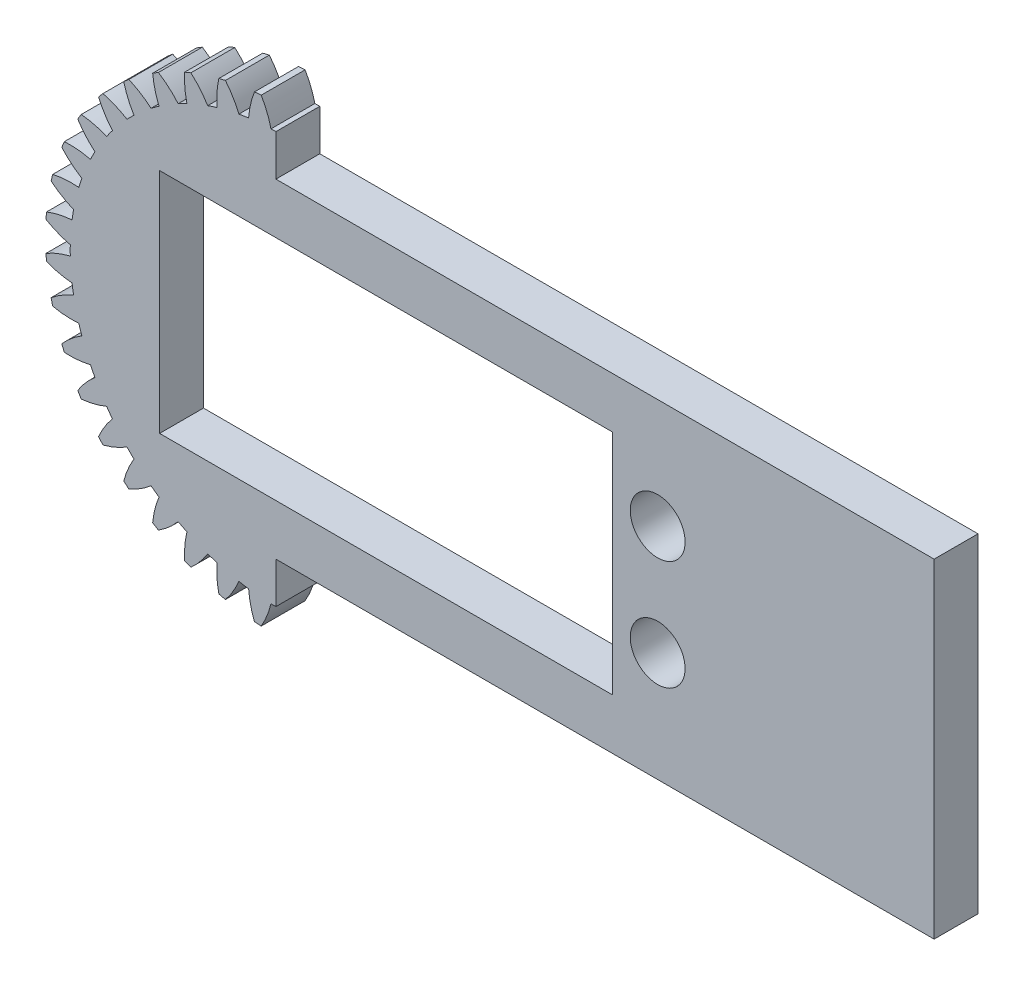
SolidWorks part; units mm, degrees
ref_plane "Front Plane" through (0, 0, 0) normal (0, 0, 1) x (1, 0, 0)
ref_plane "Top Plane" through (0, 0, 0) normal (0, 1, 0) x (1, 0, 0)
ref_plane "Right Plane" through (0, 0, 0) normal (1, 0, 0) x (0, 0, -1)
sketch "Model" plane through (0, 0, 0) normal (0, 0, 1) x (1, 0, 0)
  arc A0 (99.0731, 84.9083) -> (99.0247, 84.2939) centre (119.9819, 82.9536) ccw
  arc A1 (101.3989, 85.4426) -> (99.0731, 84.9083) centre (102.0071, 77.4658) ccw
  arc A2 (101.5392, 86.3289) -> (101.3989, 85.4426) centre (119.9819, 82.9536) ccw
  arc A3 (99.4924, 87.5558) -> (101.5392, 86.3289) centre (104.5827, 93.7274) ccw
  arc A4 (99.6363, 88.1551) -> (99.4924, 87.5558) centre (119.9819, 82.9536) ccw
  arc A5 (102.017, 88.319) -> (99.6363, 88.1551) centre (101.37, 80.3452) ccw
  arc A6 (102.2943, 89.1725) -> (102.017, 88.319) centre (119.9819, 82.9536) ccw
  arc A7 (100.4646, 90.7044) -> (102.2943, 89.1725) centre (106.4577, 96.0037) ccw
  arc A8 (100.7005, 91.2739) -> (100.4646, 90.7044) centre (119.9819, 82.9536) ccw
  arc A9 (103.0775, 91.0633) -> (100.7005, 91.2739) centre (101.1911, 83.2889) ccw
  arc A10 (103.4849, 91.8628) -> (103.0775, 91.0633) centre (119.9819, 82.9536) ccw
  arc A11 (101.9174, 93.6622) -> (103.4849, 91.8628) centre (108.6657, 97.9587) ccw
  arc A12 (102.2394, 94.1877) -> (101.9174, 93.6622) centre (119.9819, 82.9536) ccw
  arc A13 (104.5543, 93.6079) -> (102.2394, 94.1877) centre (101.4748, 86.2243) ccw
  arc A14 (105.0817, 94.3339) -> (104.5543, 93.6079) centre (119.9819, 82.9536) ccw
  arc A15 (103.815, 96.3562) -> (105.0817, 94.3339) centre (111.1523, 99.5442) ccw
  arc A16 (104.2153, 96.8249) -> (103.815, 96.3562) centre (119.9819, 82.9536) ccw
  arc A17 (106.4109, 95.8901) -> (104.2153, 96.8249) centre (102.2143, 89.0792) ccw
  arc A18 (107.0454, 96.5247) -> (106.4109, 95.8901) centre (119.9819, 82.9536) ccw
  arc A19 (106.1106, 98.7203) -> (107.0454, 96.5247) centre (113.8564, 100.7212) ccw
  arc A20 (106.5793, 99.1206) -> (106.1106, 98.7203) centre (119.9819, 82.9536) ccw
  arc A21 (108.6017, 97.8538) -> (106.5793, 99.1206) centre (103.3913, 91.7832) ccw
  arc A22 (109.3277, 98.3813) -> (108.6017, 97.8538) centre (119.9819, 82.9536) ccw
  arc A23 (108.7479, 100.6961) -> (109.3277, 98.3813) centre (116.7112, 101.4607) ccw
  arc A24 (109.2734, 101.0182) -> (108.7479, 100.6961) centre (119.9819, 82.9536) ccw
  arc A25 (111.0727, 99.4506) -> (109.2734, 101.0182) centre (104.9769, 94.2699) ccw
  arc A26 (111.8723, 99.858) -> (111.0727, 99.4506) centre (119.9819, 82.9536) ccw
  arc A27 (111.6617, 102.2351) -> (111.8723, 99.858) centre (119.6467, 101.7445) ccw
  arc A28 (112.2311, 102.471) -> (111.6617, 102.2351) centre (119.9819, 82.9536) ccw
  arc A29 (113.7631, 100.6412) -> (112.2311, 102.471) centre (106.9318, 96.4779) ccw
  arc A30 (114.6165, 100.9185) -> (113.7631, 100.6412) centre (119.9819, 82.9536) ccw
  arc A31 (114.7804, 103.2993) -> (114.6165, 100.9185) centre (122.5903, 101.5656) ccw
  arc A32 (115.3798, 103.4432) -> (114.7804, 103.2993) centre (119.9819, 82.9536) ccw
  arc A33 (116.6066, 101.3963) -> (115.3798, 103.4432) centre (109.2082, 98.3528) ccw
  arc A34 (117.4929, 101.5367) -> (116.6066, 101.3963) centre (119.9819, 82.9536) ccw
  arc A35 (118.0272, 103.8625) -> (117.4929, 101.5367) centre (125.4698, 100.9284) ccw
  arc A36 (118.6417, 103.9108) -> (118.0272, 103.8625) centre (119.9819, 82.9536) ccw
  arc A37 (119.5332, 101.6973) -> (118.6417, 103.9108) centre (111.7498, 99.8486) ccw
  arc A38 (120.4306, 101.6973) -> (119.5332, 101.6973) centre (119.9819, 82.9536) ccw
  arc A39 (121.3221, 103.9108) -> (120.4306, 101.6973) centre (128.2141, 99.8486) ccw
  arc A40 (121.9366, 103.8625) -> (121.3221, 103.9108) centre (119.9819, 82.9536) ccw
  arc A41 (122.4709, 101.5367) -> (121.9366, 103.8625) centre (114.4941, 100.9284) ccw
  arc A42 (123.3572, 101.3963) -> (122.4709, 101.5367) centre (119.9819, 82.9536) ccw
  arc A43 (124.5841, 103.4432) -> (123.3572, 101.3963) centre (130.7557, 98.3528) ccw
  arc A44 (125.1834, 103.2993) -> (124.5841, 103.4432) centre (119.9819, 82.9536) ccw
  arc A45 (125.3473, 100.9185) -> (125.1834, 103.2993) centre (117.3735, 101.5656) ccw
  arc A46 (126.2007, 100.6412) -> (125.3473, 100.9185) centre (119.9819, 82.9536) ccw
  arc A47 (127.7327, 102.471) -> (126.2007, 100.6412) centre (133.032, 96.4779) ccw
  arc A48 (128.3021, 102.2351) -> (127.7327, 102.471) centre (119.9819, 82.9536) ccw
  arc A49 (128.0916, 99.858) -> (128.3021, 102.2351) centre (120.3172, 101.7445) ccw
  arc A50 (128.8911, 99.4506) -> (128.0916, 99.858) centre (119.9819, 82.9536) ccw
  arc A51 (130.6904, 101.0182) -> (128.8911, 99.4506) centre (134.987, 94.2699) ccw
  arc A52 (131.216, 100.6961) -> (130.6904, 101.0182) centre (119.9819, 82.9536) ccw
  arc A53 (130.6362, 98.3813) -> (131.216, 100.6961) centre (123.2526, 101.4607) ccw
  arc A54 (131.3621, 97.8538) -> (130.6362, 98.3813) centre (119.9819, 82.9536) ccw
  arc A55 (133.3845, 99.1206) -> (131.3621, 97.8538) centre (136.5725, 91.7832) ccw
  arc A56 (133.8532, 98.7203) -> (133.3845, 99.1206) centre (119.9819, 82.9536) ccw
  arc A57 (132.9184, 96.5247) -> (133.8532, 98.7203) centre (126.1075, 100.7212) ccw
  arc A58 (133.5529, 95.8901) -> (132.9184, 96.5247) centre (119.9819, 82.9536) ccw
  arc A59 (135.7486, 96.8249) -> (133.5529, 95.8901) centre (137.7495, 89.0792) ccw
  arc A60 (136.1489, 96.3562) -> (135.7486, 96.8249) centre (119.9819, 82.9536) ccw
  arc A61 (134.8821, 94.3339) -> (136.1489, 96.3562) centre (128.8115, 99.5442) ccw
  arc A62 (135.4096, 93.6079) -> (134.8821, 94.3339) centre (119.9819, 82.9536) ccw
  arc A63 (137.7244, 94.1877) -> (135.4096, 93.6079) centre (138.489, 86.2243) ccw
  arc A64 (138.0465, 93.6622) -> (137.7244, 94.1877) centre (119.9819, 82.9536) ccw
  arc A65 (136.4789, 91.8628) -> (138.0465, 93.6622) centre (131.2981, 97.9587) ccw
  arc A66 (136.8863, 91.0633) -> (136.4789, 91.8628) centre (119.9819, 82.9536) ccw
  arc A67 (139.2634, 91.2739) -> (136.8863, 91.0633) centre (138.7728, 83.2889) ccw
  arc A68 (139.4992, 90.7044) -> (139.2634, 91.2739) centre (119.9819, 82.9536) ccw
  arc A69 (137.6695, 89.1725) -> (139.4992, 90.7044) centre (133.5061, 96.0037) ccw
  arc A70 (137.9468, 88.319) -> (137.6695, 89.1725) centre (119.9819, 82.9536) ccw
  arc A71 (140.3275, 88.1551) -> (137.9468, 88.319) centre (138.5939, 80.3452) ccw
  arc A72 (140.4714, 87.5558) -> (140.3275, 88.1551) centre (119.9819, 82.9536) ccw
  arc A73 (138.4246, 86.3289) -> (140.4714, 87.5558) centre (135.3811, 93.7274) ccw
  arc A74 (138.565, 85.4426) -> (138.4246, 86.3289) centre (119.9819, 82.9536) ccw
  arc A75 (140.8907, 84.9083) -> (138.565, 85.4426) centre (137.9567, 77.4658) ccw
  arc A76 (140.9391, 84.2939) -> (140.8907, 84.9083) centre (119.9819, 82.9536) ccw
  arc A77 (138.7255, 83.4023) -> (140.9391, 84.2939) centre (136.8769, 91.1858) ccw
  arc A78 (138.7255, 82.505) -> (138.7255, 83.4023) centre (119.9819, 82.9536) ccw
  arc A79 (140.9391, 81.6134) -> (138.7255, 82.505) centre (136.8769, 74.7215) ccw
  arc A80 (140.8907, 80.9989) -> (140.9391, 81.6134) centre (119.9819, 82.9536) ccw
  arc A81 (138.565, 80.4646) -> (140.8907, 80.9989) centre (137.9567, 88.4415) ccw
  arc A82 (138.4246, 79.5783) -> (138.565, 80.4646) centre (119.9819, 82.9536) ccw
  arc A83 (140.4714, 78.3515) -> (138.4246, 79.5783) centre (135.3811, 72.1799) ccw
  arc A84 (140.3275, 77.7522) -> (140.4714, 78.3515) centre (119.9819, 82.9536) ccw
  arc A85 (137.9468, 77.5883) -> (140.3275, 77.7522) centre (138.5939, 85.562) ccw
  arc A86 (137.6695, 76.7348) -> (137.9468, 77.5883) centre (119.9819, 82.9536) ccw
  arc A87 (139.4992, 75.2029) -> (137.6695, 76.7348) centre (133.5061, 69.9036) ccw
  arc A88 (139.2634, 74.6334) -> (139.4992, 75.2029) centre (119.9819, 82.9536) ccw
  arc A89 (136.8863, 74.844) -> (139.2634, 74.6334) centre (138.7728, 82.6184) ccw
  arc A90 (136.4789, 74.0444) -> (136.8863, 74.844) centre (119.9819, 82.9536) ccw
  arc A91 (138.0465, 72.2451) -> (136.4789, 74.0444) centre (131.2981, 67.9486) ccw
  arc A92 (137.7244, 71.7196) -> (138.0465, 72.2451) centre (119.9819, 82.9536) ccw
  arc A93 (135.4096, 72.2994) -> (137.7244, 71.7196) centre (138.489, 79.683) ccw
  arc A94 (134.8821, 71.5734) -> (135.4096, 72.2994) centre (119.9819, 82.9536) ccw
  arc A95 (136.1489, 69.551) -> (134.8821, 71.5734) centre (128.8115, 66.3631) ccw
  arc A96 (135.7486, 69.0824) -> (136.1489, 69.551) centre (119.9819, 82.9536) ccw
  arc A97 (133.5529, 70.0172) -> (135.7486, 69.0824) centre (137.7495, 76.8281) ccw
  arc A98 (132.9184, 69.3826) -> (133.5529, 70.0172) centre (119.9819, 82.9536) ccw
  arc A99 (133.8532, 67.187) -> (132.9184, 69.3826) centre (126.1075, 65.1861) ccw
  arc A100 (133.3845, 66.7867) -> (133.8532, 67.187) centre (119.9819, 82.9536) ccw
  arc A101 (131.3621, 68.0535) -> (133.3845, 66.7867) centre (136.5725, 74.124) ccw
  arc A102 (130.6362, 67.526) -> (131.3621, 68.0535) centre (119.9819, 82.9536) ccw
  arc A103 (131.216, 65.2112) -> (130.6362, 67.526) centre (123.2526, 64.4466) ccw
  arc A104 (130.6904, 64.8891) -> (131.216, 65.2112) centre (119.9819, 82.9536) ccw
  arc A105 (128.8911, 66.4566) -> (130.6904, 64.8891) centre (134.987, 71.6374) ccw
  arc A106 (128.0916, 66.0493) -> (128.8911, 66.4566) centre (119.9819, 82.9536) ccw
  arc A107 (128.3021, 63.6722) -> (128.0916, 66.0493) centre (120.3172, 64.1628) ccw
  arc A108 (127.7327, 63.4363) -> (128.3021, 63.6722) centre (119.9819, 82.9536) ccw
  arc A109 (126.2007, 65.266) -> (127.7327, 63.4363) centre (133.032, 69.4294) ccw
  arc A110 (125.3473, 64.9887) -> (126.2007, 65.266) centre (119.9819, 82.9536) ccw
  arc A111 (125.1834, 62.608) -> (125.3473, 64.9887) centre (117.3735, 64.3417) ccw
  arc A112 (124.5841, 62.4641) -> (125.1834, 62.608) centre (119.9819, 82.9536) ccw
  arc A113 (123.3572, 64.511) -> (124.5841, 62.4641) centre (130.7557, 67.5545) ccw
  arc A114 (122.4709, 64.3706) -> (123.3572, 64.511) centre (119.9819, 82.9536) ccw
  arc A115 (121.9366, 62.0448) -> (122.4709, 64.3706) centre (114.4941, 64.9789) ccw
  arc A116 (121.3221, 61.9965) -> (121.9366, 62.0448) centre (119.9819, 82.9536) ccw
  arc A117 (120.4306, 64.21) -> (121.3221, 61.9965) centre (128.2141, 66.0587) ccw
  arc A118 (119.5332, 64.21) -> (120.4306, 64.21) centre (119.9819, 82.9536) ccw
  arc A119 (118.6417, 61.9965) -> (119.5332, 64.21) centre (111.7498, 66.0587) ccw
  arc A120 (118.0272, 62.0448) -> (118.6417, 61.9965) centre (119.9819, 82.9536) ccw
  arc A121 (117.4929, 64.3706) -> (118.0272, 62.0448) centre (125.4698, 64.9789) ccw
  arc A122 (116.6066, 64.511) -> (117.4929, 64.3706) centre (119.9819, 82.9536) ccw
  arc A123 (115.3798, 62.4641) -> (116.6066, 64.511) centre (109.2082, 67.5545) ccw
  arc A124 (114.7804, 62.608) -> (115.3798, 62.4641) centre (119.9819, 82.9536) ccw
  arc A125 (114.6165, 64.9887) -> (114.7804, 62.608) centre (122.5903, 64.3417) ccw
  arc A126 (113.7631, 65.266) -> (114.6165, 64.9887) centre (119.9819, 82.9536) ccw
  arc A127 (112.2311, 63.4363) -> (113.7631, 65.266) centre (106.9318, 69.4294) ccw
  arc A128 (111.6617, 63.6722) -> (112.2311, 63.4363) centre (119.9819, 82.9536) ccw
  arc A129 (111.8723, 66.0493) -> (111.6617, 63.6722) centre (119.6467, 64.1628) ccw
  arc A130 (111.0727, 66.4566) -> (111.8723, 66.0493) centre (119.9819, 82.9536) ccw
  arc A131 (109.2734, 64.8891) -> (111.0727, 66.4566) centre (104.9769, 71.6374) ccw
  arc A132 (108.7479, 65.2112) -> (109.2734, 64.8891) centre (119.9819, 82.9536) ccw
  arc A133 (109.3277, 67.526) -> (108.7479, 65.2112) centre (116.7112, 64.4466) ccw
  arc A134 (108.6017, 68.0535) -> (109.3277, 67.526) centre (119.9819, 82.9536) ccw
  arc A135 (106.5793, 66.7867) -> (108.6017, 68.0535) centre (103.3913, 74.124) ccw
  arc A136 (106.1106, 67.187) -> (106.5793, 66.7867) centre (119.9819, 82.9536) ccw
  arc A137 (107.0454, 69.3826) -> (106.1106, 67.187) centre (113.8564, 65.1861) ccw
  arc A138 (106.4109, 70.0172) -> (107.0454, 69.3826) centre (119.9819, 82.9536) ccw
  arc A139 (104.2153, 69.0824) -> (106.4109, 70.0172) centre (102.2143, 76.8281) ccw
  arc A140 (103.815, 69.551) -> (104.2153, 69.0824) centre (119.9819, 82.9536) ccw
  arc A141 (105.0817, 71.5734) -> (103.815, 69.551) centre (111.1523, 66.3631) ccw
  arc A142 (104.5543, 72.2994) -> (105.0817, 71.5734) centre (119.9819, 82.9536) ccw
  arc A143 (102.2394, 71.7196) -> (104.5543, 72.2994) centre (101.4748, 79.683) ccw
  arc A144 (101.9174, 72.2451) -> (102.2394, 71.7196) centre (119.9819, 82.9536) ccw
  arc A145 (103.4849, 74.0444) -> (101.9174, 72.2451) centre (108.6657, 67.9486) ccw
  arc A146 (103.0775, 74.844) -> (103.4849, 74.0444) centre (119.9819, 82.9536) ccw
  arc A147 (100.7005, 74.6334) -> (103.0775, 74.844) centre (101.1911, 82.6184) ccw
  arc A148 (100.4646, 75.2029) -> (100.7005, 74.6334) centre (119.9819, 82.9536) ccw
  arc A149 (102.2943, 76.7348) -> (100.4646, 75.2029) centre (106.4577, 69.9036) ccw
  arc A150 (102.017, 77.5883) -> (102.2943, 76.7348) centre (119.9819, 82.9536) ccw
  arc A151 (99.6363, 77.7522) -> (102.017, 77.5883) centre (101.37, 85.562) ccw
  arc A152 (99.4924, 78.3515) -> (99.6363, 77.7522) centre (119.9819, 82.9536) ccw
  arc A153 (101.5392, 79.5783) -> (99.4924, 78.3515) centre (104.5827, 72.1799) ccw
  arc A154 (101.3989, 80.4646) -> (101.5392, 79.5783) centre (119.9819, 82.9536) ccw
  arc A155 (99.0731, 80.9989) -> (101.3989, 80.4646) centre (102.0071, 88.4415) ccw
  arc A156 (99.0247, 81.6134) -> (99.0731, 80.9989) centre (119.9819, 82.9536) ccw
  arc A157 (101.2383, 82.505) -> (99.0247, 81.6134) centre (103.0869, 74.7215) ccw
  arc A158 (101.2383, 83.4023) -> (101.2383, 82.505) centre (119.9819, 82.9536) ccw
  arc A159 (99.0247, 84.2939) -> (101.2383, 83.4023) centre (103.0869, 91.1858) ccw
  circle A160 centre (119.9819, 82.9536) radius 2.5
extrude "Boss-Extrude1" add sketch "Model" along normal blind 4
sketch "Sketch6" plane through (0, 0, 4) normal (0, 0, 1) x (1, 0, 0)
  circle A0 centre (119.9819, 82.9536) radius 11.7886
sketch "Sketch3" plane through (0, 0, 4) normal (0, 0, 1) x (1, 0, 0)
  line L0 (119.9819, 107.1901) -> (119.9819, 58.7171)
  line L1 (119.9819, 58.7171) -> (157.9977, 58.7171)
  line L2 (157.9977, 58.7171) -> (157.9977, 107.1901)
  line L3 (157.9977, 107.1901) -> (119.9819, 107.1901)
  point P4 (119.9819, 82.9536)
extrude "Cut-Extrude1" cut sketch "Sketch3" against normal blind 4
sketch "Sketch4" plane through (0, 0, 0) normal (0, 0, 1) x (1, 0, 0)
  line L0 (117.4819, 82.9536) -> (149.9819, 82.9536) construction
  line L1 (119.9819, 101.7026) -> (119.9819, 85.4536) construction
  line L2 (179.9819, 67.9536) -> (119.9819, 67.9536)
  line L3 (179.9819, 67.9536) -> (179.9819, 97.9536)
  line L4 (179.9819, 97.9536) -> (119.9819, 97.9536)
  line L5 (119.9819, 67.9536) -> (119.9819, 97.9536)
  line L6 (149.9819, 97.9536) -> (149.9819, 67.9536) construction
  line L7 (179.9819, 82.9536) -> (119.9819, 82.9536) construction
  arc A0 (119.9819, 85.4536) -> (119.9819, 80.4536) centre (119.9819, 82.9536) ccw construction
  dimension "D1" = 60
  dimension "D2" = 30
extrude "Boss-Extrude2" add sketch "Sketch4" along normal up to surface (4 mm away) up to face at (107.8896, 82.9536, 4)
sketch "Sketch7" plane through (0, 0, 4) normal (0, 0, 1) x (1, 0, 0)
  line L0 (117.4819, 82.9536) -> (179.9819, 82.9536) construction
  line L1 (179.9819, 67.9536) -> (179.9819, 97.9536) construction
  line L3 (109.8819, 72.8286) -> (150.1819, 72.8286) construction
  line L4 (109.8819, 72.8286) -> (109.8819, 92.8286) construction
  line L5 (109.8819, 92.8286) -> (150.1819, 92.8286) construction
  line L6 (150.1819, 72.8286) -> (150.1819, 92.8286) construction
  line L7 (109.3819, 93.3286) -> (150.6819, 93.3286)
  line L8 (109.3819, 93.3286) -> (109.3819, 72.5786)
  line L9 (109.3819, 72.5786) -> (150.6819, 72.5786)
  line L10 (150.6819, 93.3286) -> (150.6819, 72.5786)
  line L11 (130.0319, 72.5786) -> (130.0319, 93.3286) construction
  line L12 (109.3819, 82.9536) -> (150.6819, 82.9536) construction
  arc A0 (119.9819, 85.4536) -> (119.9819, 80.4536) centre (119.9819, 82.9536) ccw construction
  circle A1 centre (119.9819, 82.9536) radius 11.7886 construction
  point P7 (130.0319, 82.9536)
  point P11 (130.0319, 82.9536)
  dimension "D5" = 10.1
  dimension "D1" = 40.3
  dimension "D2" = 20
  dimension "D3" = 0.5
  dimension "D4" = 0.5
  dimension "D6" = 0.5
  dimension "D7" = 0.5
extrude "Cut-Extrude2" cut sketch "Sketch7" against normal blind 4
sketch "Sketch8" plane through (0, 0, 4) normal (0, 0, 1) x (1, 0, 0)
  line L0 (154.7819, 87.9536) -> (154.7819, 77.9536)
  line L1 (130.0319, 93.3286) -> (130.0319, 72.5786) construction
  line L2 (130.0319, 72.5786) -> (130.0319, 93.3286) construction
  line L4 (179.9819, 82.9536) -> (129.5819, 82.9536) construction
  circle A0 centre (154.7819, 77.9536) radius 2.5
  circle A1 centre (154.7819, 87.9536) radius 2.5
  circle A2 centre (105.2819, 87.9536) radius 2.5
  circle A3 centre (105.2819, 77.9536) radius 2.5
  point P3 (154.7819, 82.9536)
  dimension "D1" = 5
  dimension "D2" = 10
  dimension "D3" = 24.75
extrude "Cut-Extrude3" cut sketch "Sketch8" against normal blind 4
